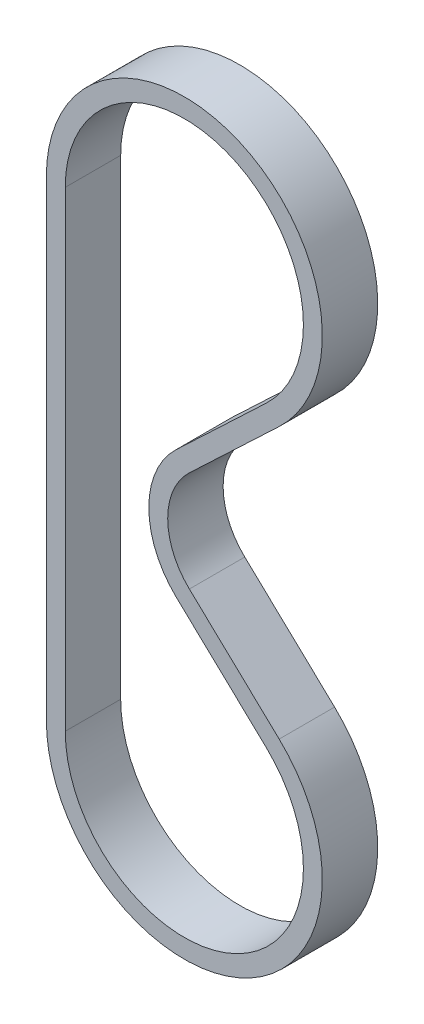
SolidWorks part; units mm, degrees
ref_plane "正面" through (0, 0, 0) normal (0, 0, 1) x (1, 0, 0)
ref_plane "平面" through (0, 0, 0) normal (0, 1, 0) x (1, 0, 0)
ref_plane "右側面" through (0, 0, 0) normal (1, 0, 0) x (0, 0, -1)
sketch "ｽｹｯﾁ1" plane through (0, 0, 0) normal (0, 0, 1) x (1, 0, 0)
  line L0 (0, 85) -> (0, 0) construction
  line L1 (0, 42.5) -> (9.5, 42.5) construction
  line L2 (-23.875, 85) -> (-23.875, 0)
  line L3 (16.4134, 67.6617) -> (0.2054, 52.3184)
  line L4 (16.4134, 17.3383) -> (0.2054, 32.6816)
  circle A0 centre (0, 0) radius 23.875 construction
  circle A1 centre (0, 85) radius 23.875 construction
  circle A2 centre (9.5, 42.5) radius 12.5 construction
  circle A3 centre (9.5, 42.5) radius 13.52 construction
  arc A4 (-23.875, 85) -> (16.4134, 67.6617) centre (0, 85) cw
  arc A5 (-23.875, 0) -> (16.4134, 17.3383) centre (0, 0) ccw
  arc A6 (0.2054, 32.6816) -> (0.2054, 52.3184) centre (9.5, 42.5) cw
  dimension "D1" = 47.75
  dimension "D2" = 47.75
  dimension "D4" = 1.02
  dimension "D5" = 25
  dimension "D3" = 85
  dimension "D6" = 9.5
extrude "押し出し-薄板1" add sketch "ｽｹｯﾁ1" along normal blind 10 thin
